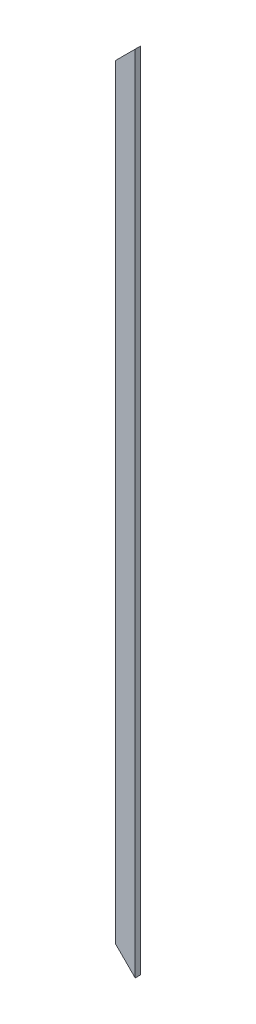
SolidWorks part; units mm, degrees
material "Oak"
ref_plane "Front Plane" through (0, 0, 0) normal (0, 0, 1) x (1, 0, 0)
ref_plane "Top Plane" through (0, 0, 0) normal (0, 1, 0) x (1, 0, 0)
ref_plane "Right Plane" through (0, 0, 0) normal (1, 0, 0) x (0, 0, -1)
sketch "Sketch1" plane through (0, 0, 0) normal (0, 1, 0) x (1, 0, 0)
  line L1 (-69.85, -19.05) -> (69.85, -19.05)
  line L2 (-69.85, -19.05) -> (-69.85, 19.05)
  line L3 (-69.85, 19.05) -> (69.85, 19.05)
  line L4 (69.85, -19.05) -> (69.85, 19.05)
  line L5 (-69.85, -19.05) -> (69.85, 19.05) construction
  line L6 (-69.85, 19.05) -> (69.85, -19.05) construction
  point P0 (0, 0)
  dimension "D1" = 38.1
  dimension "D2" = 139.7
extrude "Boss-Extrude1" add sketch "Sketch1" along normal blind 5664.2 contours L1 L4 L3 L2
sketch "Sketch2" plane through (0, 0, 19.05) normal (0, 0, 1) x (1, 0, 0)
  line L0 (69.85, 5664.2) -> (-69.85, 5524.5)
  line L1 (-69.85, 5664.2) -> (-69.85, 0) construction
  line L2 (-69.85, 5524.5) -> (-69.85, 5664.2)
  line L3 (-69.85, 5664.2) -> (69.85, 5664.2)
  line L4 (69.85, 0) -> (-69.85, 139.7)
  line L5 (-69.85, 139.7) -> (-69.85, 0)
  line L6 (-69.85, 0) -> (69.85, 0)
extrude "Cut-Extrude1" cut sketch "Sketch2" against normal through all both and the other way through all
